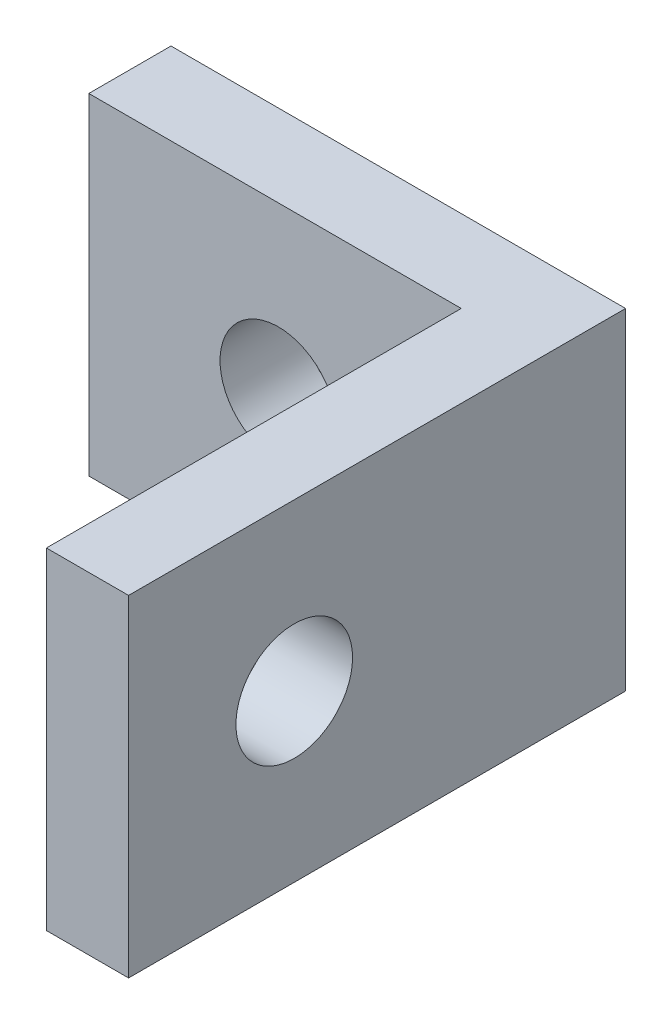
SolidWorks part; units mm, degrees
ref_plane "Front Plane" through (0, 0, 0) normal (0, 0, 1) x (1, 0, 0)
ref_plane "Top Plane" through (0, 0, 0) normal (0, 1, 0) x (1, 0, 0)
ref_plane "Right Plane" through (0, 0, 0) normal (1, 0, 0) x (0, 0, -1)
sketch "Sketch1" plane through (0, 0, 0) normal (0, 0, 1) x (1, 0, 0)
  line L1 (-4.3561, -3.175) -> (4.3561, -3.175)
  line L2 (-4.3561, -3.175) -> (-4.3561, 3.175)
  line L3 (-4.3561, 3.175) -> (4.3561, 3.175)
  line L4 (4.3561, -3.175) -> (4.3561, 3.175)
  line L5 (-4.3561, -3.175) -> (4.3561, 3.175) construction
  line L6 (-4.3561, 3.175) -> (4.3561, -3.175) construction
  point P0 (0, 0)
  dimension "D1" = 8.7122
  dimension "D2" = 6.35
extrude "Boss-Extrude1" add sketch "Sketch1" along normal blind 1.5748
sketch "Sketch2" plane through (0, 0, 1.5748) normal (0, 0, 1) x (1, 0, 0)
  line L0 (4.3561, 3.175) -> (4.3561, -3.175)
  line L1 (4.3561, -3.175) -> (2.7813, -3.175)
  line L2 (-4.3561, -3.175) -> (4.3561, -3.175) construction
  line L3 (2.7813, -3.175) -> (2.7813, 3.175)
  line L4 (4.3561, 3.175) -> (-4.3561, 3.175) construction
  line L5 (2.7813, 3.175) -> (4.3561, 3.175)
  dimension "D1" = 1.5748
extrude "Boss-Extrude2" add sketch "Sketch2" along normal blind 7.9502
sketch "Sketch3" plane through (0, 0, 1.5748) normal (0, 0, 1) x (1, 0, 0)
  line L1 (4.3561, -3.175) -> (4.3561, 3.175) construction
  circle A0 centre (-0.7239, 0) radius 1.1176
  dimension "D1" = 2.2352
  dimension "D2" = 5.08
extrude "Cut-Extrude1" cut sketch "Sketch3" against normal through all
sketch "Sketch4" plane through (4.3561, 0, 0) normal (1, 0, 0) x (0, 0, -1)
  line L0 (0, 0) -> (-9.525, 0) construction
  line L1 (0, -3.175) -> (0, 3.175) construction
  line L2 (-9.525, -3.175) -> (-9.525, 3.175) construction
  circle A0 centre (-6.35, 0) radius 1.1176
  dimension "D1" = 2.2352
  dimension "D2" = 6.35
extrude "Cut-Extrude2" cut sketch "Sketch4" against normal through all
